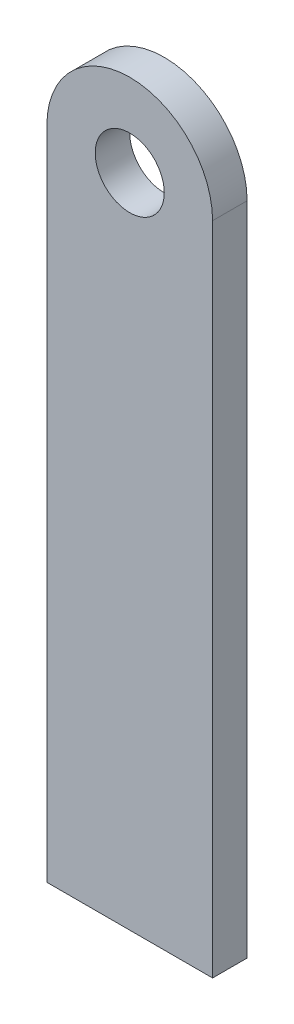
SolidWorks part; units mm, degrees
ref_plane "Front Plane" through (0, 0, 0) normal (0, 0, 1) x (1, 0, 0)
ref_plane "Top Plane" through (0, 0, 0) normal (0, 1, 0) x (1, 0, 0)
ref_plane "Right Plane" through (0, 0, 0) normal (1, 0, 0) x (0, 0, -1)
sketch "Sketch1" plane through (0, 0, 0) normal (0, 0, 1) x (1, 0, 0)
  line L0 (0, 0) -> (0, -60.325) construction
  line L1 (-7.62, 0) -> (-7.62, -60.325)
  line L2 (-7.62, -60.325) -> (7.62, -60.325)
  line L3 (7.62, -60.325) -> (7.62, 0)
  circle A0 centre (0, 0) radius 3.175
  arc A1 (7.62, 0) -> (-7.62, 0) centre (0, 0) ccw
  dimension "D1" = 6.35
  dimension "D2" = 15.24
  dimension "D3" = 60.325
extrude "Boss-Extrude1" add sketch "Sketch1" along normal blind 3.175
